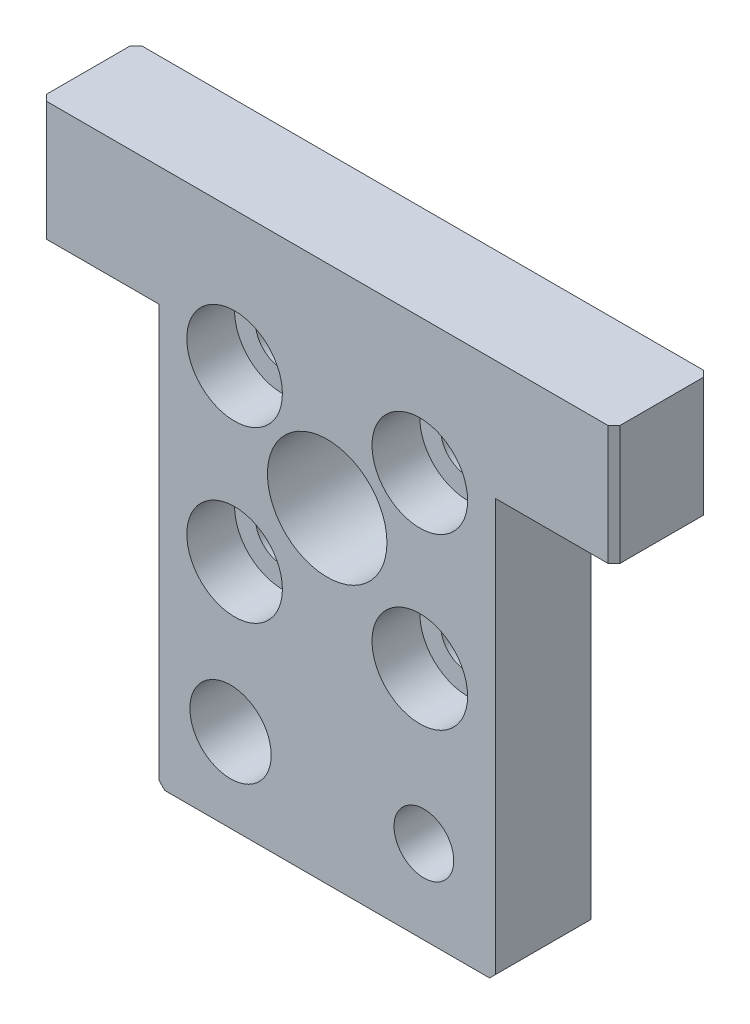
SolidWorks part; units mm, degrees
ref_plane "Front Plane" through (0, 0, 0) normal (0, 0, 1) x (1, 0, 0)
ref_plane "Top Plane" through (0, 0, 0) normal (0, 1, 0) x (1, 0, 0)
ref_plane "Right Plane" through (0, 0, 0) normal (1, 0, 0) x (0, 0, -1)
sketch "Sketch1" plane through (0, 0, 0) normal (0, 0, 1) x (1, 0, 0)
  line L0 (21.2537, 11.6418) -> (31.1642, 11.6418)
  line L1 (-16.8358, 21.6418) -> (31.1642, 21.6418)
  line L2 (-16.8358, 21.6418) -> (-16.8358, 11.6418)
  line L3 (-16.8358, 11.6418) -> (-6.9254, 11.6418)
  line L4 (31.1642, 21.6418) -> (31.1642, 11.6418)
  line L6 (21.2537, 11.6418) -> (21.2537, -23.3582)
  line L7 (21.2537, -23.3582) -> (-6.9254, -23.3582)
  line L8 (-6.9254, 11.6418) -> (-6.9254, -23.3582)
  circle A0 centre (7.1642, 3.8918) radius 5
  circle A1 centre (-0.5858, -3.8582) radius 2.25
  circle A2 centre (14.9142, -3.8582) radius 2.25
  circle A3 centre (14.9142, 10.3284) radius 2.25
  circle A4 centre (-0.5858, 10.3284) radius 2.25
  point P18 (7.1642, 21.6418)
  point P19 (0, 0)
  point P20 (0, 0)
  point P21 (0, 0)
  point P22 (0, 0)
  dimension "D7" = 10
  dimension "D8" = 4.5
  dimension "D1" = 48
  dimension "D2" = 10
  dimension "D3" = 45
  dimension "D4" = 16.25
  dimension "D5" = 31.75
  dimension "D6" = 25.5
  dimension "D9" = 17.75
extrude "Boss-Extrude1" add sketch "Sketch1" along normal blind 8
sketch "Sketch2" plane through (0, 0, 8) normal (0, 0, 1) x (1, 0, 0)
  circle A0 centre (-0.5858, 10.3284) radius 4
  circle A1 centre (14.9142, 10.3284) radius 4
  circle A2 centre (14.9142, -3.8582) radius 4
  circle A3 centre (-0.5858, -3.8582) radius 4
  dimension "D1" = 8
extrude "Cut-Extrude1" cut sketch "Sketch2" against normal blind 4
hole_wizard "M6 Tapped Hole1" positions "Sketch3" profile "Sketch4" tap size "M6" standard "ISO"
sketch "Sketch3" plane through (0, 0, 8) normal (0, 0, 1) x (1, 0, 0)
  line L0 (21.2537, -23.3582) -> (21.2537, 11.6418) construction
  line L1 (31.1642, 21.6418) -> (-16.8358, 21.6418) construction
  point P0 (15.2537, -16.3582)
  dimension "D1" = 6
  dimension "D2" = 38
sketch "Sketch4" plane through (15.2537, -16.3582, 8) normal (1, 0, 0) x (0, -1, 0)
  line L0 (0, 0) -> (0, 16.5022)
  line L1 (0, 16.5022) -> (2.5, 15)
  line L2 (2.5, 15) -> (2.5, 0)
  line L5 (2.5, 0) -> (0, 0)
  line L10 (0, 16.5022) -> (-2.5, 15) construction
  line L11 (0, -6.35) -> (0, 107.95) construction
  dimension "Tap Drill Dia." = 5
  dimension "Tap Drill Depth" = 15
  dimension "Drill Angle" = 118
cosmetic thread "Hole Thread1" parameters "D1"=8, "D2"=6
hole_wizard "M8 Tapped Hole1" positions "Sketch5" profile "Sketch6" tap size "M8" standard "ISO"
sketch "Sketch5" plane through (0, 0, 8) normal (0, 0, 1) x (1, 0, 0)
  line L0 (31.1642, 21.6418) -> (-16.8358, 21.6418) construction
  line L1 (-6.9254, 11.6418) -> (-6.9254, -23.3582) construction
  point P0 (-0.9254, -16.3582)
  dimension "D1" = 38
  dimension "D2" = 6
sketch "Sketch6" plane through (-0.9254, -16.3582, 8) normal (1, 0, 0) x (0, -1, 0)
  line L0 (0, 0) -> (0, 21.7929)
  line L1 (0, 21.7929) -> (3.4, 19.75)
  line L2 (3.4, 19.75) -> (3.4, 0)
  line L5 (3.4, 0) -> (0, 0)
  line L10 (0, 21.7929) -> (-3.4, 19.75) construction
  line L11 (0, -6.35) -> (0, 107.95) construction
  dimension "Tap Drill Dia." = 6.8
  dimension "Tap Drill Depth" = 19.75
  dimension "Drill Angle" = 118
cosmetic thread "Hole Thread2" parameters "D1"=8, "D2"=8
chamfer "Chamfer1" distance 0.5 angle 45 4 edges at (31.1642, 16.6418, 8) (31.1642, 16.6418, 0) (-16.8358, 16.6418, 0) (-16.8358, 16.6418, 8)
chamfer "Chamfer2" distance 0.5 angle 45 2 edges at (-6.9254, -23.3582, 4) (21.2537, -23.3582, 4)
